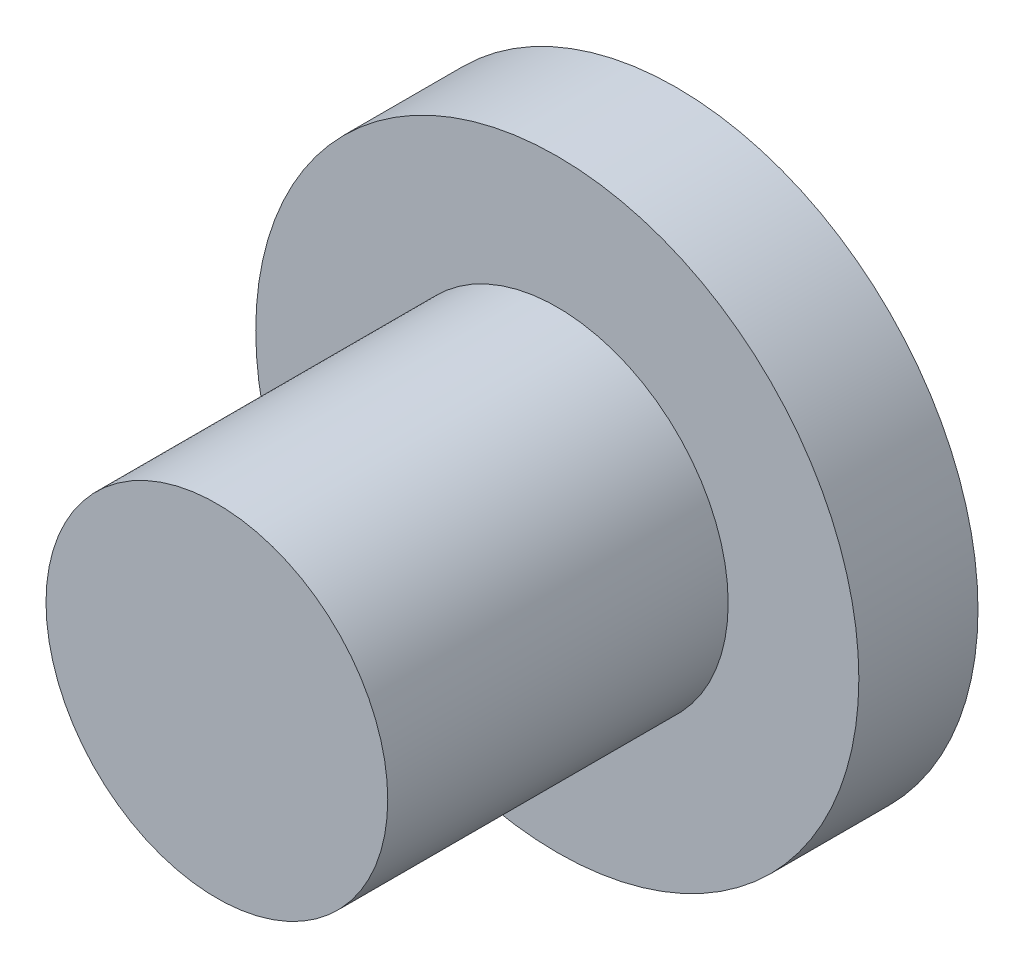
SolidWorks part; units mm, degrees
ref_plane "Front Plane" through (0, 0, 0) normal (0, 0, 1) x (1, 0, 0)
ref_plane "Top Plane" through (0, 0, 0) normal (0, 1, 0) x (1, 0, 0)
ref_plane "Right Plane" through (0, 0, 0) normal (1, 0, 0) x (0, 0, -1)
sketch "Sketch1" plane through (0, 0, 0) normal (0, 0, 1) x (1, 0, 0)
  circle A0 centre (-10.0603, 7.7464) radius 4.5
extrude "Boss-Extrude2" add sketch "Sketch1" along normal blind 1.778
sketch "Sketch2" plane through (0, 0, 1.778) normal (0, 0, 1) x (1, 0, 0)
  line L0 (-10.8947, 12.1684) -> (-10.0603, 7.7464) construction
  line L1 (-10.0603, 7.7464) -> (-9.2259, 3.3244) construction
  circle A0 centre (-10.0603, 7.7464) radius 4.5 construction
  circle A1 centre (-10.0603, 7.7464) radius 2.55
extrude "Boss-Extrude4" add sketch "Sketch2" along normal blind 5.08
